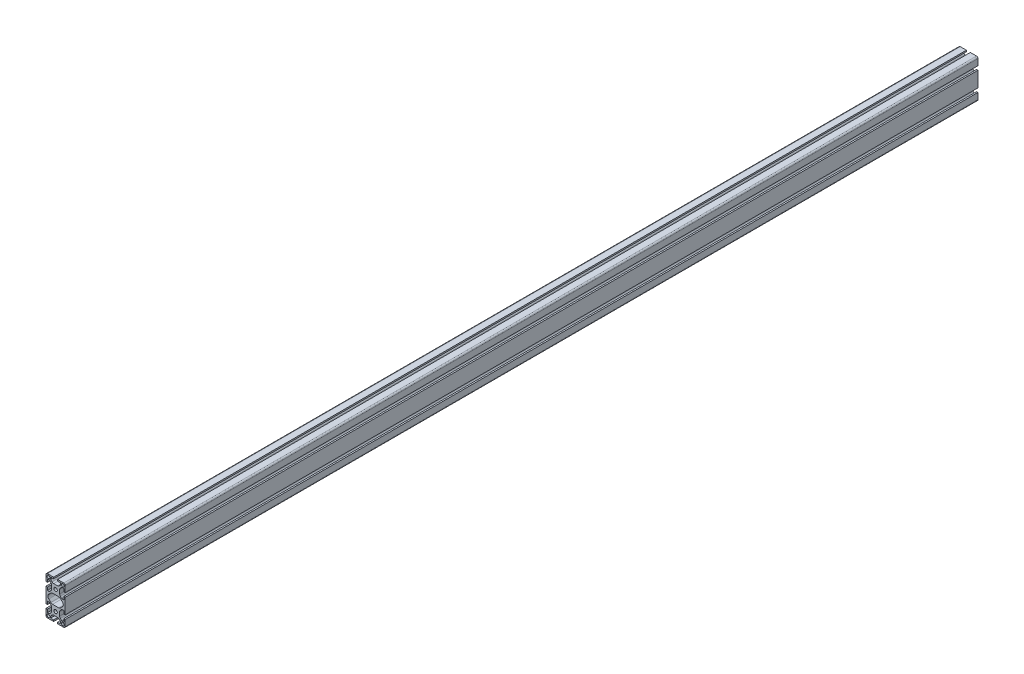
SolidWorks part; units mm, degrees
ref_plane "Front Plane" through (0, 0, 0) normal (0, 0, 1) x (1, 0, 0)
ref_plane "Top Plane" through (0, 0, 0) normal (0, 1, 0) x (1, 0, 0)
ref_plane "Right Plane" through (0, 0, 0) normal (1, 0, 0) x (0, 0, -1)
sketch "Sketch1" plane through (0, 0, 0) normal (0, 0, 1) x (1, 0, 0)
  line L0 (-17, -40) -> (-4.1, -40)
  line L1 (-4.1, -40) -> (-4.1, -37)
  line L2 (-4.1, -37) -> (-10.5, -37)
  line L3 (-10.5, -37) -> (-10.5, -33.6627)
  line L4 (-10.0314, -32.5314) -> (-7.4645, -29.9645)
  line L5 (-3.9289, -28.5) -> (3.9289, -28.5)
  line L6 (7.4645, -29.9645) -> (10.0314, -32.5314)
  line L7 (10.5, -33.6627) -> (10.5, -37)
  line L8 (10.5, -37) -> (4.1, -37)
  line L9 (4.1, -37) -> (4.1, -40)
  line L10 (4.1, -40) -> (17, -40)
  line L11 (20, -37) -> (20, -24.1)
  line L12 (20, -24.1) -> (17, -24.1)
  line L13 (17, -24.1) -> (17, -30.5)
  line L14 (17, -30.5) -> (13.6627, -30.5)
  line L15 (12.5314, -30.0314) -> (9.9645, -27.4645)
  line L16 (8.5, -23.9289) -> (8.5, -16.0711)
  line L17 (9.9645, -12.5355) -> (12.5314, -9.9686)
  line L18 (13.6627, -9.5) -> (17, -9.5)
  line L19 (17, -9.5) -> (17, -15.9)
  line L20 (17, -15.9) -> (20, -15.9)
  line L21 (20, -15.9) -> (20, 15.9)
  line L22 (20, 15.9) -> (17, 15.9)
  line L23 (17, 15.9) -> (17, 9.5)
  line L24 (17, 9.5) -> (13.6627, 9.5)
  line L25 (12.5314, 9.9686) -> (9.9645, 12.5355)
  line L26 (8.5, 16.0711) -> (8.5, 23.9289)
  line L27 (9.9645, 27.4645) -> (12.5314, 30.0314)
  line L28 (13.6627, 30.5) -> (17, 30.5)
  line L29 (17, 30.5) -> (17, 24.1)
  line L30 (17, 24.1) -> (20, 24.1)
  line L31 (20, 24.1) -> (20, 37)
  line L32 (17, 40) -> (4.1, 40)
  line L33 (4.1, 40) -> (4.1, 37)
  line L34 (4.1, 37) -> (10.5, 37)
  line L35 (10.5, 37) -> (10.5, 33.6627)
  line L36 (10.0314, 32.5314) -> (7.4645, 29.9645)
  line L37 (3.9289, 28.5) -> (-3.9289, 28.5)
  line L38 (-7.4645, 29.9645) -> (-10.0314, 32.5314)
  line L39 (-10.5, 33.6627) -> (-10.5, 37)
  line L40 (-10.5, 37) -> (-4.1, 37)
  line L41 (-4.1, 37) -> (-4.1, 40)
  line L42 (-4.1, 40) -> (-17, 40)
  line L43 (-20, 37) -> (-20, 24.1)
  line L44 (-20, 24.1) -> (-17, 24.1)
  line L45 (-17, 24.1) -> (-17, 30.5)
  line L46 (-17, 30.5) -> (-13.6627, 30.5)
  line L47 (-12.5314, 30.0314) -> (-9.9645, 27.4645)
  line L48 (-8.5, 23.9289) -> (-8.5, 16.0711)
  line L49 (-9.9645, 12.5355) -> (-12.5314, 9.9686)
  line L50 (-13.6627, 9.5) -> (-17, 9.5)
  line L51 (-17, 9.5) -> (-17, 15.9)
  line L52 (-17, 15.9) -> (-20, 15.9)
  line L53 (-20, 15.9) -> (-20, -15.9)
  line L54 (-20, -15.9) -> (-17, -15.9)
  line L55 (-17, -15.9) -> (-17, -9.5)
  line L56 (-17, -9.5) -> (-13.6627, -9.5)
  line L57 (-12.5314, -9.9686) -> (-9.9645, -12.5355)
  line L58 (-8.5, -16.0711) -> (-8.5, -23.9289)
  line L59 (-9.9645, -27.4645) -> (-12.5314, -30.0314)
  line L60 (-13.6627, -30.5) -> (-17, -30.5)
  line L61 (-17, -30.5) -> (-17, -24.1)
  line L62 (-17, -24.1) -> (-20, -24.1)
  line L63 (-20, -24.1) -> (-20, -37)
  line L64 (-14.2426, -4.2426) -> (-9.9497, -8.5355)
  line L65 (-6.4142, -10) -> (6.4142, -10)
  line L66 (9.9497, -8.5355) -> (14.2426, -4.2426)
  line L67 (14.2426, 4.2426) -> (9.9497, 8.5355)
  line L68 (6.4142, 10) -> (-6.4142, 10)
  line L69 (-9.9497, 8.5355) -> (-14.2426, 4.2426)
  arc A0 (-20, -37) -> (-17, -40) centre (-17, -37) ccw
  arc A1 (-10.5, -33.6627) -> (-10.0314, -32.5314) centre (-8.9, -33.6627) cw
  arc A2 (-7.4645, -29.9645) -> (-3.9289, -28.5) centre (-3.9289, -33.5) cw
  arc A3 (3.9289, -28.5) -> (7.4645, -29.9645) centre (3.9289, -33.5) cw
  arc A4 (10.0314, -32.5314) -> (10.5, -33.6627) centre (8.9, -33.6627) cw
  arc A5 (17, -40) -> (20, -37) centre (17, -37) ccw
  arc A6 (13.6627, -30.5) -> (12.5314, -30.0314) centre (13.6627, -28.9) cw
  arc A7 (9.9645, -27.4645) -> (8.5, -23.9289) centre (13.5, -23.9289) cw
  arc A8 (8.5, -16.0711) -> (9.9645, -12.5355) centre (13.5, -16.0711) cw
  arc A9 (12.5314, -9.9686) -> (13.6627, -9.5) centre (13.6627, -11.1) cw
  arc A10 (13.6627, 9.5) -> (12.5314, 9.9686) centre (13.6627, 11.1) cw
  arc A11 (9.9645, 12.5355) -> (8.5, 16.0711) centre (13.5, 16.0711) cw
  arc A12 (8.5, 23.9289) -> (9.9645, 27.4645) centre (13.5, 23.9289) cw
  arc A13 (12.5314, 30.0314) -> (13.6627, 30.5) centre (13.6627, 28.9) cw
  arc A14 (20, 37) -> (17, 40) centre (17, 37) ccw
  arc A15 (10.5, 33.6627) -> (10.0314, 32.5314) centre (8.9, 33.6627) cw
  arc A16 (7.4645, 29.9645) -> (3.9289, 28.5) centre (3.9289, 33.5) cw
  arc A17 (-3.9289, 28.5) -> (-7.4645, 29.9645) centre (-3.9289, 33.5) cw
  arc A18 (-10.0314, 32.5314) -> (-10.5, 33.6627) centre (-8.9, 33.6627) cw
  arc A19 (-17, 40) -> (-20, 37) centre (-17, 37) ccw
  arc A20 (-13.6627, 30.5) -> (-12.5314, 30.0314) centre (-13.6627, 28.9) cw
  arc A21 (-9.9645, 27.4645) -> (-8.5, 23.9289) centre (-13.5, 23.9289) cw
  arc A22 (-8.5, 16.0711) -> (-9.9645, 12.5355) centre (-13.5, 16.0711) cw
  arc A23 (-12.5314, 9.9686) -> (-13.6627, 9.5) centre (-13.6627, 11.1) cw
  arc A24 (-13.6627, -9.5) -> (-12.5314, -9.9686) centre (-13.6627, -11.1) cw
  arc A25 (-9.9645, -12.5355) -> (-8.5, -16.0711) centre (-13.5, -16.0711) cw
  arc A26 (-8.5, -23.9289) -> (-9.9645, -27.4645) centre (-13.5, -23.9289) cw
  arc A27 (-12.5314, -30.0314) -> (-13.6627, -30.5) centre (-13.6627, -28.9) cw
  circle A28 centre (15, 35) radius 3
  circle A29 centre (15, -35) radius 3
  circle A30 centre (0, 20) radius 3.5
  circle A31 centre (0, -20) radius 3.5
  arc A32 (-14.2426, 4.2426) -> (-14.2426, -4.2426) centre (-10, 0) ccw
  arc A33 (-9.9497, -8.5355) -> (-6.4142, -10) centre (-6.4142, -5) ccw
  arc A34 (6.4142, -10) -> (9.9497, -8.5355) centre (6.4142, -5) ccw
  arc A35 (14.2426, -4.2426) -> (14.2426, 4.2426) centre (10, 0) ccw
  arc A36 (9.9497, 8.5355) -> (6.4142, 10) centre (6.4142, 5) ccw
  arc A37 (-6.4142, 10) -> (-9.9497, 8.5355) centre (-6.4142, 5) ccw
  circle A38 centre (-15, 35) radius 3
  circle A39 centre (-15, -35) radius 3
  dimension "D3" = 6
  dimension "D4" = 6
  dimension "D5" = 6
  dimension "D6" = 6
  dimension "D7" = 7
  dimension "D8" = 7
  dimension "D1" = 40
  dimension "D2" = 80
extrude "Boss-Extrude1" add sketch "Sketch1" against normal blind 1900
